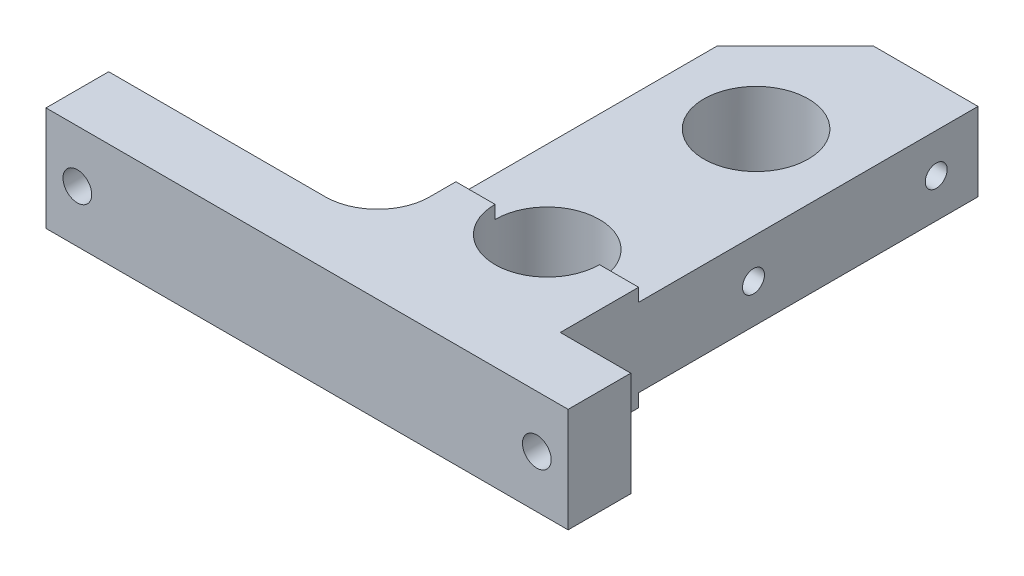
SolidWorks part; units mm, degrees
ref_plane "Front Plane" through (0, 0, 0) normal (0, 0, 1) x (1, 0, 0)
ref_plane "Top Plane" through (0, 0, 0) normal (0, 1, 0) x (1, 0, 0)
ref_plane "Right Plane" through (0, 0, 0) normal (1, 0, 0) x (0, 0, -1)
sketch "Sketch1" plane through (0, 0, 0) normal (0, 0, 1) x (1, 0, 0)
  line L1 (-50, 10) -> (50, 10)
  line L2 (-50, 10) -> (-50, -10)
  line L3 (-50, -10) -> (50, -10)
  line L4 (50, 10) -> (50, -10)
  line L5 (-50, 10) -> (50, -10) construction
  line L6 (-50, -10) -> (50, 10) construction
  point P0 (0, 0)
  dimension "D1" = 100
  dimension "D2" = 20
extrude "Boss-Extrude1" add sketch "Sketch1" along normal blind 12
sketch "Sketch2" plane through (0, 0, 0) normal (0, 0, -1) x (-1, 0, 0)
  line L0 (50, -10) -> (-50, -10) construction
  line L1 (-1.5, -10) -> (-36.5, -10)
  line L2 (-1.5, -10) -> (-1.5, 10)
  line L3 (-1.5, 10) -> (-36.5, 10)
  line L4 (-36.5, -10) -> (-36.5, 10)
  line L5 (-1.5, -10) -> (-36.5, 10) construction
  line L6 (-1.5, 10) -> (-36.5, -10) construction
  line L7 (-50, -10) -> (-50, 10) construction
  point P0 (-19, 0)
  dimension "D1" = 0
  dimension "D2" = 20
  dimension "D3" = 13.5
  dimension "D4" = 35
extrude "Boss-Extrude3" add sketch "Sketch2" along normal blind 15
sketch "Sketch3" plane through (0, 0, -15) normal (0, 0, -1) x (-1, 0, 0)
  line L0 (-1.5, -10) -> (-1.5, 10) construction
  line L1 (-1.5, -7.5) -> (-36.5, -7.5)
  line L2 (-1.5, -7.5) -> (-1.5, 7.5)
  line L3 (-1.5, 7.5) -> (-36.5, 7.5)
  line L4 (-36.5, -7.5) -> (-36.5, 7.5)
  line L5 (-36.5, 10) -> (-36.5, -10) construction
  line L6 (-36.5, -10) -> (-1.5, -10) construction
  line L7 (-1.5, 10) -> (-36.5, 10) construction
  dimension "D1" = 2.5
  dimension "D2" = 2.5
extrude "Boss-Extrude4" add sketch "Sketch3" along normal blind 65
fillet "Fillet1" radius 10 1 edges at (1.5, 0, 0)
chamfer "Chamfer1" distance 15 angle 45 1 edges at (1.5, 0, -80)
sketch "Sketch4" plane through (0, 7.5, 0) normal (0, 1, 0) x (1, 0, 0)
  line L0 (50, -12) -> (-50, -12) construction
  line L1 (50, -12) -> (50, 0) construction
  circle A0 centre (19, 15) radius 10
  circle A1 centre (19, 55) radius 10
  point P4 (0, 0)
  dimension "D1" = 20
  dimension "D2" = 67
  dimension "D3" = 27
  dimension "D4" = 31
extrude "Cut-Extrude1" cut sketch "Sketch4" against normal blind 65 and the other way blind 65
hole_wizard "M5 Tapped Hole1" positions "Sketch5" profile "Sketch6" tap size "M5" standard "ISO"
sketch "Sketch5" plane through (36.5, 0, 0) normal (1, 0, 0) x (0, 0, -1)
  line L0 (-12, -10) -> (-12, 10) construction
  point P0 (72, 0)
  point P2 (37, 0)
  dimension "D1" = 84
  dimension "D2" = 49
sketch "Sketch6" plane through (36.5, 0, -72) normal (0, 1, 0) x (0, 0, -1)
  line L0 (0, 0) -> (0, 11.2618)
  line L1 (0, 11.2618) -> (2.1, 10)
  line L2 (2.1, 10) -> (2.1, 0)
  line L5 (2.1, 0) -> (0, 0)
  line L10 (0, 11.2618) -> (-2.1, 10) construction
  line L11 (0, -6.35) -> (0, 107.95) construction
  dimension "Tap Drill Dia." = 4.2
  dimension "Tap Drill Depth" = 10
  dimension "Drill Angle" = 118
cosmetic thread "Hole Thread1" parameters "D1"=10, "D2"=5
cosmetic thread "Hole Thread2" parameters "D1"=10, "D2"=5
sketch "Sketch7" plane through (0, 0, 0) normal (0, 0, -1) x (-1, 0, 0)
  line L0 (-50, -10) -> (-50, 10) construction
  circle A0 centre (44, 0) radius 2.75
  circle A1 centre (-44, 0) radius 2.75
  point P4 (0, 0)
  dimension "D1" = 5.5
  dimension "D2" = 6
  dimension "D3" = 94
extrude "Cut-Extrude2" cut sketch "Sketch7" against normal blind 65
